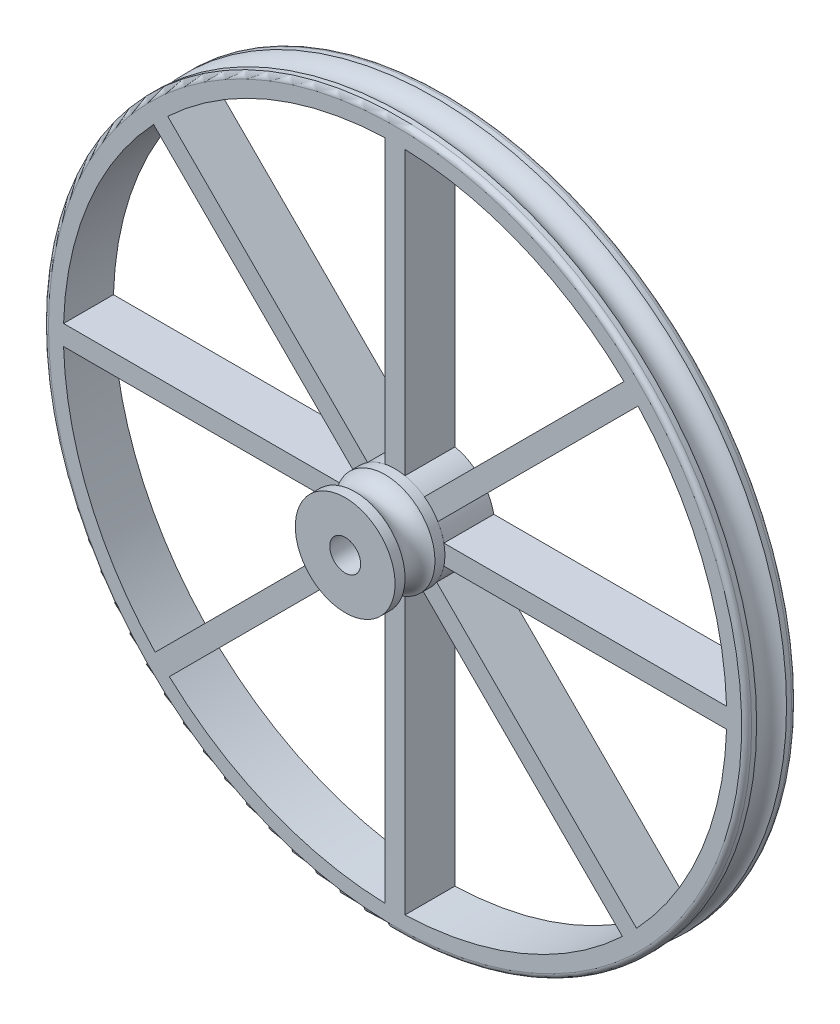
SolidWorks part; units mm, degrees
ref_plane "Front Plane" through (0, 0, 0) normal (0, 0, 1) x (1, 0, 0)
ref_plane "Top Plane" through (0, 0, 0) normal (0, 1, 0) x (1, 0, 0)
ref_plane "Right Plane" through (0, 0, 0) normal (1, 0, 0) x (0, 0, -1)
sketch "Sketch1" plane through (0, 0, 0) normal (0, 0, 1) x (1, 0, 0)
  circle A0 centre (0, 0) radius 29.75
  circle A1 centre (0, 0) radius 1.65
  dimension "D1" = 59.5
  dimension "D2" = 3.3
sketch "Sketch4" plane through (0, 0, 0) normal (1, 0, 0) x (0, 0, -1)
  line L0 (-5, 35.25) -> (-4, 35.25)
  line L1 (55, 0) -> (-55, 0) construction
  line L3 (0, 35.25) -> (-1, 35.25)
  line L7 (0, 35.25) -> (0, 0)
  line L8 (-5, 35.25) -> (-5, 0)
  line L10 (-5, 0) -> (0, 0)
  line L11 (0, 55) -> (0, -55) construction
  arc A0 (-4, 35.25) -> (-1, 35.25) centre (-2.5, 35.875) ccw
  point P15 (-2.5, 34.25)
  dimension "D2" = 35.25
  dimension "D1" = 1
  dimension "D3" = 1
revolve "Revolve1" add sketch "Sketch4" angle 360 about L10
sketch "Sketch6" plane through (0, 0, 0) normal (1, 0, 0) x (0, 0, -1)
  line L0 (-5, 0) -> (-5, 5)
  line L1 (-5, 5) -> (-6, 5)
  line L2 (-9, 5) -> (-10, 5)
  line L3 (-10, 5) -> (-10, 0)
  line L4 (-10, 0) -> (-5, 0)
  line L5 (-5, 35.25) -> (-5, -35.25) construction
  line L6 (55, 0) -> (-55, 0) construction
  arc A0 (-6, 5) -> (-9, 5) centre (-7.5, 5.625) cw
  point P8 (-7.5, 4)
  dimension "D1" = 1
  dimension "D2" = 1
  dimension "D3" = 5
  dimension "D4" = 5
revolve "Revolve2" add sketch "Sketch6" angle 360 about L4
sketch "Sketch7" plane through (0, 0, 0) normal (0, 0, 1) x (1, 0, 0)
  circle A0 centre (0, 0) radius 1.55
  dimension "D1" = 3.1
extrude "Cut-Extrude1" cut sketch "Sketch7" along normal blind 10
sketch "Sketch8" plane through (0, 0, 0) normal (0, 0, 1) x (1, 0, 0)
  line L10 (4.899, 1) -> (33.235, 1)
  line L11 (1, 4.899) -> (1, 33.235)
  line L12 (4.899, -1) -> (33.235, -1)
  line L13 (1, -4.899) -> (1, -33.235)
  line L14 (-1, -33.235) -> (-1, -4.899)
  line L15 (-33.235, -1) -> (-4.899, -1)
  line L16 (-33.235, 1) -> (-4.899, 1)
  line L17 (-1, 4.899) -> (-1, 33.235)
  line L18 (-22.4274, 22.4274) -> (22.4274, -22.4274) construction
  line L19 (0, 42.9618) -> (0, -48.1055) construction
  line L20 (-40.9984, 0) -> (49.712, 0) construction
  line L21 (5.5, 0) -> (-5.5, 0) construction
  line L22 (24.2078, -22.7936) -> (4.1712, -2.757)
  line L23 (-31.6023, -31.9162) -> (33.3304, 33.0165) construction
  line L24 (22.9547, 24.055) -> (2.9423, 4.0426)
  line L25 (24.3595, 22.6314) -> (4.2924, 2.5643)
  line L26 (-24.055, -22.9547) -> (-4.0426, -2.9423)
  line L27 (-22.6314, -24.3595) -> (-2.5643, -4.2924)
  line L28 (22.7936, -24.2078) -> (2.757, -4.1712)
  line L29 (-24.2078, 22.7936) -> (-4.1712, 2.757)
  line L30 (-22.7936, 24.2078) -> (-2.757, 4.1712)
  circle A1 centre (0, 0) radius 33.25 construction
  circle A12 centre (0, 0) radius 5 construction
  arc A13 (-22.7936, 24.2078) -> (-1, 33.235) centre (0, 0) cw
  arc A14 (1, 33.235) -> (22.9547, 24.055) centre (0, 0) cw
  arc A15 (24.3595, 22.6314) -> (33.235, 1) centre (0, 0) cw
  arc A16 (33.235, -1) -> (24.2078, -22.7936) centre (0, 0) cw
  arc A17 (22.7936, -24.2078) -> (1, -33.235) centre (0, 0) cw
  arc A18 (-1, -33.235) -> (-22.6314, -24.3595) centre (0, 0) cw
  arc A19 (-24.055, -22.9547) -> (-33.235, -1) centre (0, 0) cw
  arc A20 (-33.235, 1) -> (-24.2078, 22.7936) centre (0, 0) cw
  arc A21 (1, 4.899) -> (2.9423, 4.0426) centre (0, 0) ccw construction
  arc A22 (4.2924, 2.5643) -> (4.899, 1) centre (0, 0) cw
  arc A23 (4.899, -1) -> (4.1712, -2.757) centre (0, 0) cw
  arc A24 (2.757, -4.1712) -> (1, -4.899) centre (0, 0) cw
  arc A25 (-1, -4.899) -> (-2.5643, -4.2924) centre (0, 0) cw
  arc A26 (-4.0426, -2.9423) -> (-4.899, -1) centre (0, 0) cw
  arc A27 (-4.899, 1) -> (-4.1712, 2.757) centre (0, 0) cw
  arc A28 (-2.757, 4.1712) -> (-1, 4.899) centre (0, 0) cw
  arc A30 (1, 4.899) -> (2.9423, 4.0426) centre (0, 0) cw
  point P39 (0.864, 0.5502)
  point P48 (0, 0)
  dimension "D1" = 66.5
  dimension "D2" = 10
  dimension "D3" = 2
  dimension "D4" = 2
  dimension "D5" = 2
  dimension "D6" = 2
  dimension "D7" = 45
  dimension "D8" = 45
  dimension "D9" = 2
  dimension "D10" = 2
  dimension "D11" = 2
  dimension "D12" = 2
extrude "Cut-Extrude2" cut sketch "Sketch8" along normal blind 5
fillet "Fillet1" radius 0.5 2 edges at (35.25, 0, 0) (35.25, 0, 5)
